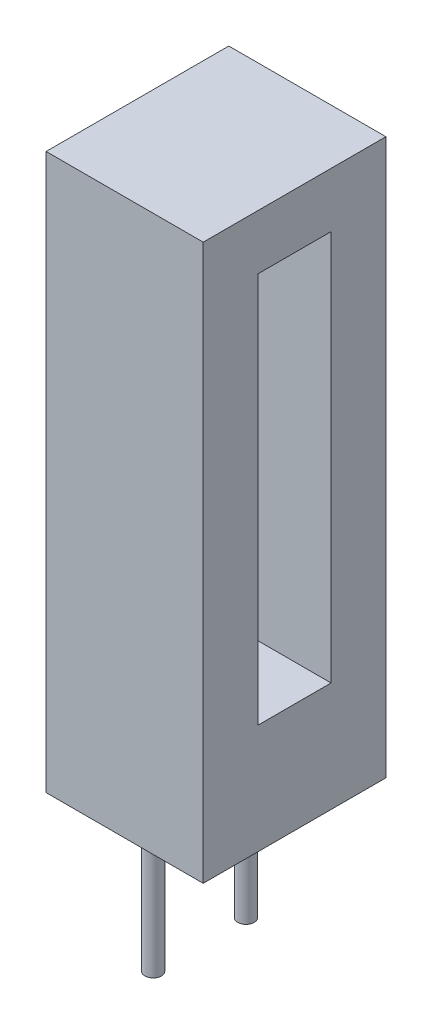
SolidWorks part; units mm, degrees
ref_plane "Front Plane" through (0, 0, 0) normal (0, 0, 1) x (1, 0, 0)
ref_plane "Top Plane" through (0, 0, 0) normal (0, 1, 0) x (1, 0, 0)
ref_plane "Right Plane" through (0, 0, 0) normal (1, 0, 0) x (0, 0, -1)
sketch "Sketch1" plane through (0, 0, 0) normal (0, 0, 1) x (1, 0, 0)
  line L0 (0, 0) -> (4.3, 0)
  line L1 (4.3, 0) -> (4.3, 15.2)
  line L2 (4.3, 15.2) -> (0, 15.2)
  line L3 (0, 15.2) -> (0, 0)
  dimension "D1" = 4.3
  dimension "D2" = 15.2
extrude "Boss-Extrude1" add sketch "Sketch1" along normal blind 5
sketch "Sketch2" plane through (4.3, 0, 0) normal (1, 0, 0) x (0, 0, -1)
  line L0 (-3.5, 3) -> (-3.5, 13.7)
  line L1 (-3.5, 13.7) -> (-1.5, 13.7)
  line L2 (-1.5, 13.7) -> (-1.5, 3)
  line L3 (-1.5, 3) -> (-3.5, 3)
  line L4 (-5, 0) -> (0, 0) construction
  line L5 (-5, 0) -> (-5, 15.2) construction
  line L6 (-5, 15.2) -> (0, 15.2) construction
  line L7 (0, 0) -> (0, 15.2) construction
  point P10 (-2.5, 15.2)
  dimension "D1" = 3
  dimension "D2" = 1.5
  dimension "D3" = 1.5
  dimension "D4" = 1.5
extrude "Cut-Extrude1" cut sketch "Sketch2" against normal blind 2
sketch "Sketch3" plane through (0, 0, 0) normal (0, -1, 0) x (1, 0, 0)
  line L0 (0, 2.5) -> (4.3, 2.5) construction
  line L1 (0, 5) -> (0, 0) construction
  line L2 (4.3, 5) -> (4.3, 0) construction
  line L3 (0, 0) -> (4.3, 0) construction
  circle A0 centre (1.7, 1.23) radius 0.225
  circle A1 centre (1.7, 3.77) radius 0.225
  dimension "D1" = 0.45
  dimension "D2" = 1.23
  dimension "D3" = 1.7
extrude "Boss-Extrude2" add sketch "Sketch3" along normal blind 4
